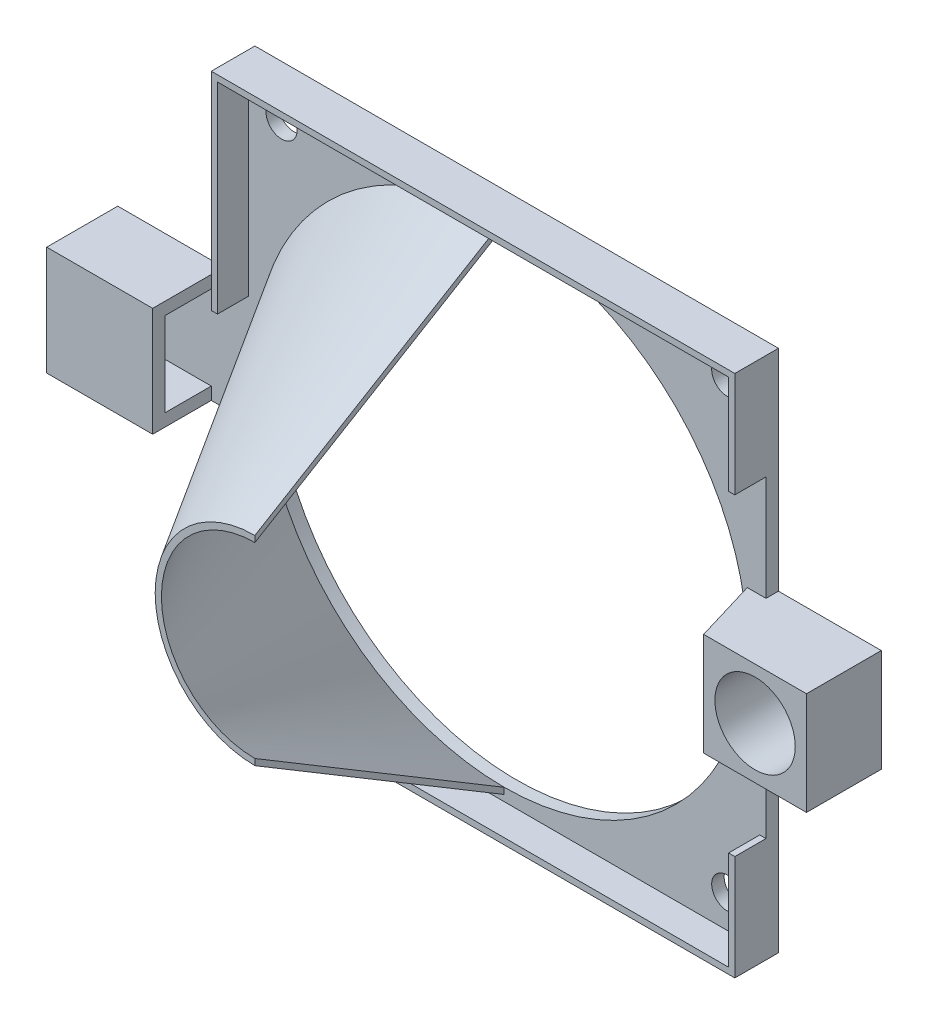
SolidWorks part; units mm, degrees
ref_plane "Alzado" through (0, 0, 0) normal (0, 0, 1) x (1, 0, 0)
ref_plane "Planta" through (0, 0, 0) normal (0, 1, 0) x (1, 0, 0)
ref_plane "Vista lateral" through (0, 0, 0) normal (1, 0, 0) x (0, 0, -1)
sketch "Croquis1" plane through (0, 0, 0) normal (0, 0, 1) x (1, 0, 0)
  line L0 (-103.3198, -49.5061) -> (-19.3198, 34.4939) construction
  line L1 (-103.3198, 34.4939) -> (-19.3198, 34.4939)
  line L2 (-103.3198, 34.4939) -> (-103.3198, -49.5061)
  line L3 (-103.3198, -49.5061) -> (-19.3198, -49.5061)
  line L4 (-19.3198, 34.4939) -> (-19.3198, -49.5061)
  line L5 (-19.3198, -49.5061) -> (-103.3198, 34.4939) construction
  circle A0 centre (-61.3198, -7.5061) radius 39
  circle A1 centre (-97.0287, 28.2028) radius 2.5
  circle A2 centre (-25.5287, 28.2028) radius 2.5
  circle A3 centre (-25.5287, -43.2972) radius 2.5
  circle A4 centre (-97.0287, -43.2972) radius 2.5
  dimension "D3" = 50.5
  dimension "D4" = 2
  dimension "D1" = 84
  dimension "D2" = 84
  dimension "D5" = 2
extrude "Saliente-Extruir1" add sketch "Croquis1" along normal blind 2
ref_plane "Plano1" through (-61.3198, -49.5061, 2) normal (1, 0, 0) x (0, 0, -1)
sketch "Croquis4" plane through (-61.3198, -49.5061, 2) normal (1, 0, 0) x (0, 0, -1)
  line L0 (0, 3) -> (0, 42) construction
  line L1 (0, 42) -> (-40, 42) construction
  line L2 (-40, 42) -> (-40, 27) construction
  line L3 (-40, 27) -> (0, 3)
  line L4 (0, 3) -> (0, 2)
  line L5 (0, 2) -> (-40, 26)
  line L6 (-40, 26) -> (-40, 27)
revolve "Revolución2" add sketch "Croquis4" angle 180 about L1
sketch "Croquis6" plane through (-103.3198, 0, 0) normal (-1, 0, 0) x (0, 0, 1)
  line L0 (0, -7.5061) -> (0, -16.2561)
  line L1 (0, 34.4939) -> (0, -49.5061) construction
  line L2 (0, -16.2561) -> (2, -16.2561)
  line L3 (2, 34.4939) -> (2, -49.5061) construction
  line L4 (2, -16.2561) -> (2, 1.2439)
  line L5 (2, 1.2439) -> (0, 1.2439)
  line L6 (0, 1.2439) -> (0, -7.5061)
extrude "Saliente-Extruir2" add sketch "Croquis6" along normal blind 20
sketch "Croquis7" plane through (-123.3198, 0, 0) normal (-1, 0, 0) x (0, 0, 1)
  line L0 (2, 1.2439) -> (2, -0.7561) construction
  line L1 (2, 1.2439) -> (11.4, 1.2439)
  line L2 (2, 1.2439) -> (2, -16.2561)
  line L3 (2, -16.2561) -> (11.4, -16.2561)
  line L4 (11.4, 1.2439) -> (11.4, -16.2561)
  line L5 (2, -16.2561) -> (2, -14.2561) construction
  line L7 (2, -0.7561) -> (9.4, -0.7561)
  line L8 (2, -0.7561) -> (2, -14.2561)
  line L9 (2, -14.2561) -> (9.4, -14.2561)
  line L10 (9.4, -0.7561) -> (9.4, -14.2561)
  line M6 (2, -16.2561) -> (2, 1.2439)
  dimension "D1" = 9.4
  dimension "D2" = 2
extrude "Saliente-Extruir3" add sketch "Croquis7" against normal blind 15 contours L7 L10 L9 L3 L4 L1 L2 M6
sketch "Croquis8" plane through (-123.3198, 0, 0) normal (-1, 0, 0) x (0, 0, 1)
  line L0 (11.4, -16.2561) -> (0, 1.2439) construction
  line L1 (0, 1.2439) -> (11.4, 1.2439)
  line L2 (0, 1.2439) -> (0, -16.2561)
  line L3 (0, -16.2561) -> (11.4, -16.2561)
  line L4 (11.4, 1.2439) -> (11.4, -16.2561)
  line L5 (11.4, 1.2439) -> (0, -16.2561) construction
  circle A0 centre (5.7, -7.5061) radius 3.6
extrude "Saliente-Extruir4" add sketch "Croquis8" along normal blind 2
sketch "Croquis9" plane through (-19.3198, 0, 0) normal (1, 0, 0) x (0, 0, -1)
  line L0 (0, -7.5061) -> (0, 0.7439)
  line L1 (0, -49.5061) -> (0, 34.4939) construction
  line L2 (0, 0.7439) -> (-2, 0.7439)
  line L3 (-2, -49.5061) -> (-2, 34.4939) construction
  line L4 (-2, 0.7439) -> (-2, -15.7561)
  line L5 (-2, -15.7561) -> (0, -15.7561)
  line L6 (0, -15.7561) -> (0, -7.5061)
extrude "Saliente-Extruir5" add sketch "Croquis9" along normal blind 16.5
sketch "Croquis10" plane through (0, 0, 2) normal (0, 0, 1) x (1, 0, 0)
  line L0 (-2.8198, -15.7561) -> (-19.3198, 0.7439) construction
  line L1 (-19.3198, -15.7561) -> (-2.8198, -15.7561)
  line L2 (-19.3198, -15.7561) -> (-19.3198, 0.7439)
  line L3 (-19.3198, 0.7439) -> (-2.8198, 0.7439)
  line L4 (-2.8198, -15.7561) -> (-2.8198, 0.7439)
  line L5 (-2.8198, 0.7439) -> (-19.3198, -15.7561) construction
  circle A0 centre (-11.0698, -7.5061) radius 6.45
extrude "Saliente-Extruir6" add sketch "Croquis10" along normal blind 10
sketch "Croquis11" plane through (0, 0.7439, 0) normal (0, 1, 0) x (1, 0, 0)
  line L0 (-19.3198, -12) -> (-19.3198, -2)
  line L1 (-19.3198, -2) -> (-22.3198, -2)
  line L2 (-22.3198, -2) -> (-19.3198, -12)
extrude "Saliente-Extruir7" add sketch "Croquis11" against normal up to vertex
sketch "Croquis12" plane through (0, 0, 2) normal (0, 0, 1) x (1, 0, 0)
  line L0 (-19.3198, 17.6189) -> (-19.3198, 34.4939)
  line L1 (-19.3198, 0.7439) -> (-19.3198, 34.4939) construction
  line L2 (-19.3198, 34.4939) -> (-103.3198, 34.4939)
  line L3 (-103.3198, 34.4939) -> (-103.3198, 1.2439)
  line L4 (-103.3198, 1.2439) -> (-102.3198, 1.2439)
  line L5 (-102.3198, 1.2439) -> (-102.3198, 33.4939)
  line L6 (-102.3198, 33.4939) -> (-20.3198, 33.4939)
  line L7 (-20.3198, 33.4939) -> (-20.3198, 17.6189)
  line L8 (-20.3198, 17.6189) -> (-19.3198, 17.6189)
  line L9 (-22.3198, -7.5061) -> (-101.3198, -7.5061) construction
  line L10 (-20.3198, -32.6311) -> (-19.3198, -32.6311)
  line L11 (-20.3198, -48.5061) -> (-20.3198, -32.6311)
  line L12 (-102.3198, -48.5061) -> (-20.3198, -48.5061)
  line L13 (-102.3198, -16.2561) -> (-102.3198, -48.5061)
  line L14 (-103.3198, -16.2561) -> (-102.3198, -16.2561)
  line L15 (-19.3198, -32.6311) -> (-19.3198, -49.5061)
  arc A0 (-61.3198, 32.4939) -> (-61.3198, -47.5061) centre (-61.3198, -7.5061) ccw construction
  line M21 (-103.3198, -16.2561) -> (-103.3198, -49.5061)
  line M22 (-103.3198, -49.5061) -> (-19.3198, -49.5061)
  line M23 (-19.3198, -49.5061) -> (-19.3198, -15.7561)
extrude "Saliente-Extruir8" add sketch "Croquis12" along normal blind 5 contours L14 L10 L11 L12 L13 M21 M22 M23 | L2 L3 L4 L5 L6 L7 L8 L0
sketch "Croquis13" plane through (0, 0, 2) normal (0, 0, 1) x (1, 0, 0)
  circle A0 centre (-11.0698, -7.5061) radius 2.5
extrude "Cortar-Extruir1" cut sketch "Croquis13" against normal up to vertex (2 mm away)
